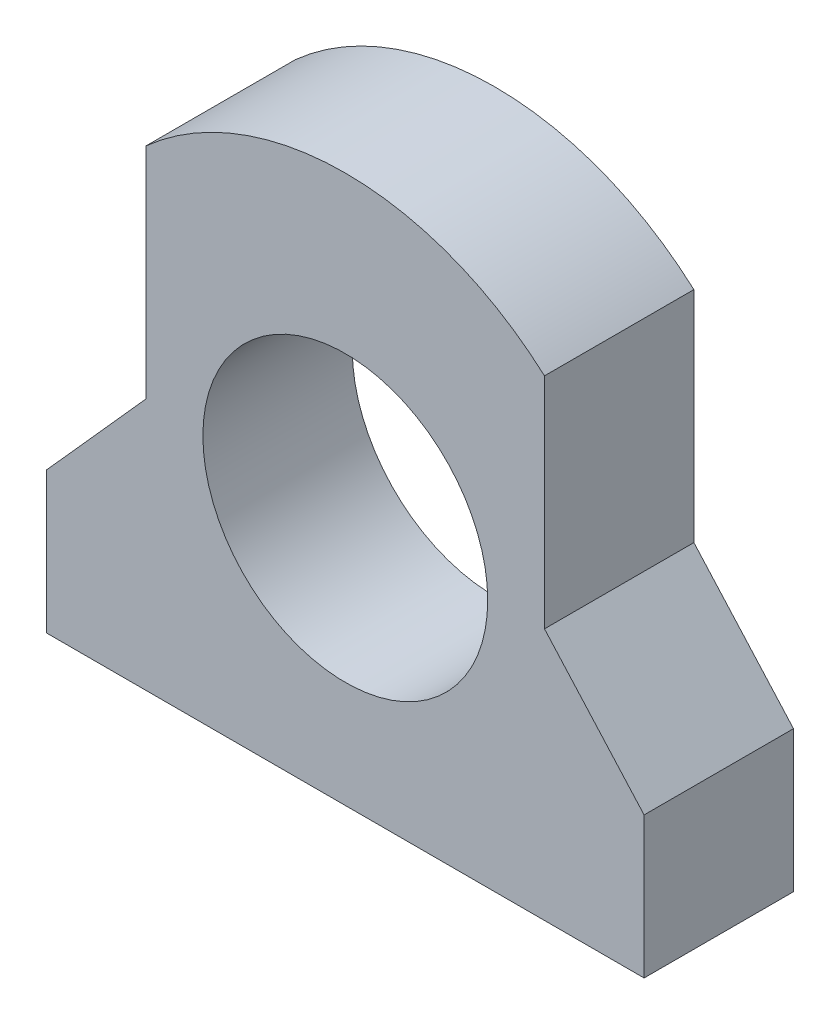
SolidWorks part; units mm, degrees
ref_plane "Front Plane" through (0, 0, 0) normal (0, 0, 1) x (1, 0, 0)
ref_plane "Top Plane" through (0, 0, 0) normal (0, 1, 0) x (1, 0, 0)
ref_plane "Right Plane" through (0, 0, 0) normal (1, 0, 0) x (0, 0, -1)
sketch "Sketch1" plane through (0, 0, 0) normal (0, 0, 1) x (1, 0, 0)
  line L0 (-30, 0) -> (30, 0)
  line L1 (-30, 0) -> (-30, 14.1803)
  line L2 (-30, 14.1803) -> (-20, 25.3607)
  line L3 (30, 0) -> (30, 14.1803)
  line L4 (30, 14.1803) -> (20, 25.3607)
  line L5 (-20, 25.3607) -> (-20, 47.3607)
  line L6 (20, 25.3607) -> (20, 47.3607)
  arc A0 (-20, 47.3607) -> (20, 47.3607) centre (0, 25) cw
  circle A1 centre (0, 25) radius 14.3
  point P3 (0, 0)
  point P7 (0, 24.7777)
  point P13 (-20.6461, 26.6767)
  point P14 (-20.6461, 46.9382)
  point P15 (-20.1404, 26.245)
  point P16 (0, 27.3505)
  dimension "D4" = 28.6
  dimension "D5" = 30
  dimension "D8" = 25
  dimension "D1" = 60
  dimension "D2" = 15
  dimension "D3" = 15
  dimension "D6" = 22
  dimension "D7" = 40
extrude "Boss-Extrude1" add sketch "Sketch1" along normal blind 15
